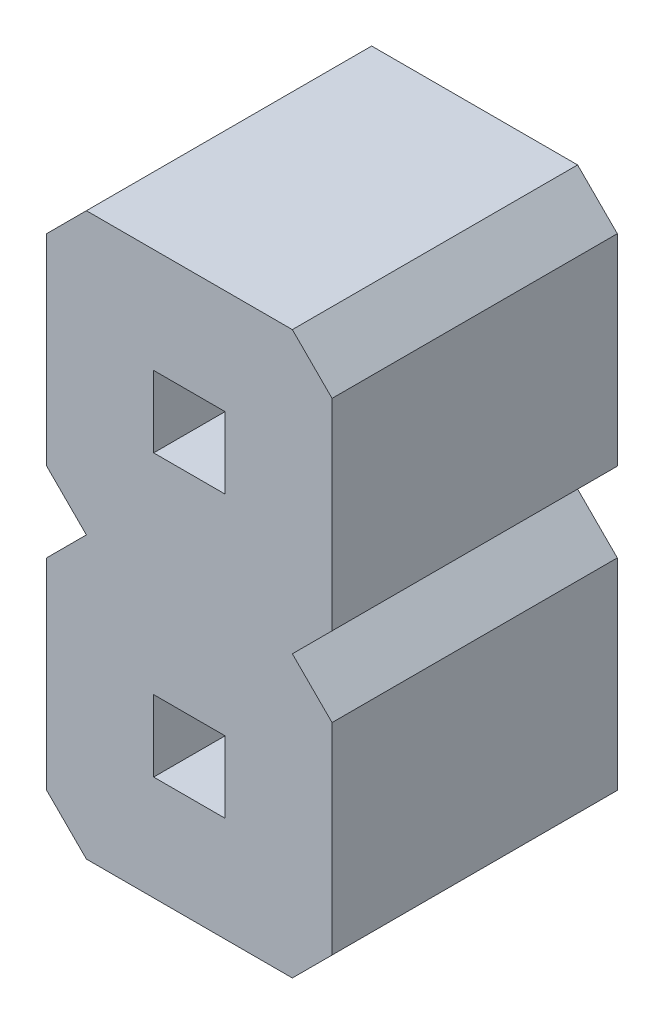
SolidWorks part; units mm, degrees
ref_plane "Alzado" through (0, 0, 0) normal (0, 0, 1) x (1, 0, 0)
ref_plane "Planta" through (0, 0, 0) normal (0, 1, 0) x (1, 0, 0)
ref_plane "Vista lateral" through (0, 0, 0) normal (1, 0, 0) x (0, 0, -1)
sketch "pin_body" plane through (0, 0, 0) normal (0, 0, 1) x (1, 0, 0)
  line L0 (0.9525, -0.932) -> (0, -0.932) construction
  line L1 (0, 2.1464) -> (0, 0.3536)
  line L2 (0, -0.3536) -> (0, -2.1464)
  line L3 (0, -0.3536) -> (0.3536, 0)
  line L4 (1.5885, -1.568) -> (2.541, -1.568) construction
  line L5 (0, 2.1464) -> (0.3536, 2.5)
  line L6 (2.541, -0.3536) -> (2.541, -2.1464)
  line L7 (0.9525, -1.25) -> (0.9525, -0.932) construction
  line L8 (2.541, -2.1464) -> (2.1874, -2.5)
  line L9 (2.1874, 0) -> (2.541, -0.3536)
  line L10 (1.5885, -1.25) -> (1.5885, -1.568) construction
  line L11 (0.3536, -2.5) -> (0, -2.1464)
  line L12 (0.9525, -0.932) -> (1.5885, -0.932)
  line L13 (0.9525, -0.932) -> (0.9525, -1.568)
  line L14 (0.9525, -1.568) -> (1.5885, -1.568)
  line L15 (1.5885, -0.932) -> (1.5885, -1.568)
  line L16 (2.541, 2.1464) -> (2.541, 0.3536)
  line L17 (2.541, 0.3536) -> (2.1874, 0)
  line L18 (2.1874, 2.5) -> (2.541, 2.1464)
  line L19 (0.3536, 0) -> (0, 0.3536)
  line L20 (0.9525, 1.568) -> (1.5885, 1.568)
  line L21 (0.9525, 1.568) -> (0.9525, 0.932)
  line L22 (0.9525, 0.932) -> (1.5885, 0.932)
  line L23 (1.5885, 1.568) -> (1.5885, 0.932)
  line L24 (0.9525, 1.568) -> (0, 1.568) construction
  line L25 (1.5885, 0.932) -> (2.541, 0.932) construction
  line L26 (0.9525, 1.25) -> (0.9525, 1.568) construction
  line L27 (1.5885, 1.25) -> (1.5885, 0.932) construction
  line L28 (0.3536, 2.5) -> (2.1874, 2.5)
  line L168 (2.1874, -2.5) -> (0.3536, -2.5)
  line L170 (0, 17.1464) -> (0, 15.3536) [skipped]
  line L171 (0, 17.1464) -> (0.3536, 17.5) [skipped]
  line L172 (2.541, 17.1464) -> (2.541, 15.3536) [skipped]
  line L173 (2.541, 15.3536) -> (2.1874, 15) [skipped]
  line L174 (2.1874, 17.5) -> (2.541, 17.1464) [skipped]
  line L175 (0.9525, 16.568) -> (1.5885, 16.568) [skipped]
  line L176 (0.9525, 16.568) -> (0.9525, 15.932) [skipped]
  line L177 (0.9525, 15.932) -> (1.5885, 15.932) [skipped]
  line L178 (1.5885, 16.568) -> (1.5885, 15.932) [skipped]
  line L179 (0, 19.6464) -> (0, 17.8536) [skipped]
  line L180 (0, 19.6464) -> (0.3536, 20) [skipped]
  line L181 (2.541, 19.6464) -> (2.541, 17.8536) [skipped]
  line L182 (2.541, 17.8536) -> (2.1874, 17.5) [skipped]
  line L183 (2.1874, 20) -> (2.541, 19.6464) [skipped]
  line L184 (0.3536, 17.5) -> (0, 17.8536) [skipped]
  line L185 (0.9525, 19.068) -> (1.5885, 19.068) [skipped]
  line L186 (0.9525, 19.068) -> (0.9525, 18.432) [skipped]
  line L187 (0.9525, 18.432) -> (1.5885, 18.432) [skipped]
  line L188 (1.5885, 19.068) -> (1.5885, 18.432) [skipped]
  line L189 (0, 22.1464) -> (0, 20.3536) [skipped]
  line L190 (0, 22.1464) -> (0.3536, 22.5) [skipped]
  line L191 (2.541, 22.1464) -> (2.541, 20.3536) [skipped]
  line L192 (2.541, 20.3536) -> (2.1874, 20) [skipped]
  line L193 (2.1874, 22.5) -> (2.541, 22.1464) [skipped]
  line L194 (0.3536, 20) -> (0, 20.3536) [skipped]
  line L195 (0.9525, 21.568) -> (1.5885, 21.568) [skipped]
  line L196 (0.9525, 21.568) -> (0.9525, 20.932) [skipped]
  line L197 (0.9525, 20.932) -> (1.5885, 20.932) [skipped]
  line L198 (1.5885, 21.568) -> (1.5885, 20.932) [skipped]
  line L199 (0, 24.6464) -> (0, 22.8536) [skipped]
  line L200 (0, 24.6464) -> (0.3536, 25) [skipped]
  line L201 (2.541, 24.6464) -> (2.541, 22.8536) [skipped]
  line L202 (2.541, 22.8536) -> (2.1874, 22.5) [skipped]
  line L203 (2.1874, 25) -> (2.541, 24.6464) [skipped]
  line L204 (0.3536, 22.5) -> (0, 22.8536) [skipped]
  line L205 (0.9525, 24.068) -> (1.5885, 24.068) [skipped]
  line L206 (0.9525, 24.068) -> (0.9525, 23.432) [skipped]
  line L207 (0.9525, 23.432) -> (1.5885, 23.432) [skipped]
  line L208 (1.5885, 24.068) -> (1.5885, 23.432) [skipped]
  line L209 (0, 27.1464) -> (0, 25.3536) [skipped]
  line L210 (0, 27.1464) -> (0.3536, 27.5) [skipped]
  line L211 (2.541, 27.1464) -> (2.541, 25.3536) [skipped]
  line L212 (2.541, 25.3536) -> (2.1874, 25) [skipped]
  line L213 (2.1874, 27.5) -> (2.541, 27.1464) [skipped]
  line L214 (0.3536, 25) -> (0, 25.3536) [skipped]
  line L215 (0.9525, 26.568) -> (1.5885, 26.568) [skipped]
  line L216 (0.9525, 26.568) -> (0.9525, 25.932) [skipped]
  line L217 (0.9525, 25.932) -> (1.5885, 25.932) [skipped]
  line L218 (1.5885, 26.568) -> (1.5885, 25.932) [skipped]
  line L219 (0.9525, 16.568) -> (0, 16.568) construction
  line L220 (1.5885, 15.932) -> (2.541, 15.932) construction
  line L221 (0.9525, 16.25) -> (0.9525, 16.568) construction
  line L222 (1.5885, 16.25) -> (1.5885, 15.932) construction
  line L223 (0.9525, 19.068) -> (0, 19.068) construction
  line L224 (1.5885, 18.432) -> (2.541, 18.432) construction
  line L225 (0.9525, 18.75) -> (0.9525, 19.068) construction
  line L226 (1.5885, 18.75) -> (1.5885, 18.432) construction
  line L227 (0.9525, 21.568) -> (0, 21.568) construction
  line L228 (1.5885, 20.932) -> (2.541, 20.932) construction
  line L229 (0.9525, 21.25) -> (0.9525, 21.568) construction
  line L230 (1.5885, 21.25) -> (1.5885, 20.932) construction
  line L231 (0.9525, 24.068) -> (0, 24.068) construction
  line L232 (1.5885, 23.432) -> (2.541, 23.432) construction
  line L233 (0.9525, 23.75) -> (0.9525, 24.068) construction
  line L234 (1.5885, 23.75) -> (1.5885, 23.432) construction
  line L235 (0.9525, 26.568) -> (0, 26.568) construction
  line L236 (1.5885, 25.932) -> (2.541, 25.932) construction
  line L237 (0.9525, 26.25) -> (0.9525, 26.568) construction
  line L238 (1.5885, 26.25) -> (1.5885, 25.932) construction
  line L239 (0, 14.6464) -> (0.3536, 15) [skipped]
  line L240 (2.1874, 15) -> (2.541, 14.6464) [skipped]
  line L241 (0.9525, 14.068) -> (1.5885, 14.068) [skipped]
  line L242 (0.9525, 14.068) -> (0.9525, 13.432) [skipped]
  line L243 (0.9525, 13.432) -> (1.5885, 13.432) [skipped]
  line L244 (1.5885, 14.068) -> (1.5885, 13.432) [skipped]
  line L245 (0.3536, 15) -> (0, 15.3536) [skipped]
  line L246 (0.9525, 14.068) -> (0, 14.068) construction
  line L247 (0.9525, 13.75) -> (0.9525, 14.068) construction
  line L248 (1.5885, 13.75) -> (1.5885, 13.432) construction
  line L249 (2.541, 14.6464) -> (2.541, 12.8536) [skipped]
  line L250 (2.541, 12.8536) -> (2.1874, 12.5) [skipped]
  line L251 (1.5885, 13.432) -> (2.541, 13.432) construction
  line L252 (0, 14.6464) -> (0, 12.8536) [skipped]
  line L253 (0.3536, 12.5) -> (0, 12.8536) [skipped]
  line L254 (0, 7.1464) -> (0.3536, 7.5) [skipped]
  line L255 (0, 9.6464) -> (0, 7.8536) [skipped]
  line L256 (0, 9.6464) -> (0.3536, 10) [skipped]
  line L257 (2.1874, 10) -> (2.541, 9.6464) [skipped]
  line L258 (0.3536, 7.5) -> (0, 7.8536) [skipped]
  line L259 (0.9525, 9.068) -> (1.5885, 9.068) [skipped]
  line L260 (0.9525, 9.068) -> (0.9525, 8.432) [skipped]
  line L261 (0.9525, 8.432) -> (1.5885, 8.432) [skipped]
  line L262 (1.5885, 9.068) -> (1.5885, 8.432) [skipped]
  line L263 (0, 12.1464) -> (0, 10.3536) [skipped]
  line L264 (0, 12.1464) -> (0.3536, 12.5) [skipped]
  line L265 (2.541, 12.1464) -> (2.541, 10.3536) [skipped]
  line L266 (2.541, 10.3536) -> (2.1874, 10) [skipped]
  line L267 (2.1874, 12.5) -> (2.541, 12.1464) [skipped]
  line L268 (0.3536, 10) -> (0, 10.3536) [skipped]
  line L269 (0.9525, 11.568) -> (1.5885, 11.568) [skipped]
  line L270 (0.9525, 11.568) -> (0.9525, 10.932) [skipped]
  line L271 (0.9525, 10.932) -> (1.5885, 10.932) [skipped]
  line L272 (1.5885, 11.568) -> (1.5885, 10.932) [skipped]
  line L273 (0.9525, 9.068) -> (0, 9.068) construction
  line L274 (0.9525, 8.75) -> (0.9525, 9.068) construction
  line L275 (1.5885, 8.75) -> (1.5885, 8.432) construction
  line L276 (0.9525, 11.568) -> (0, 11.568) construction
  line L277 (1.5885, 10.932) -> (2.541, 10.932) construction
  line L278 (0.9525, 11.25) -> (0.9525, 11.568) construction
  line L279 (1.5885, 11.25) -> (1.5885, 10.932) construction
  line L280 (0, 7.1464) -> (0, 5.3536) [skipped]
  line L281 (2.541, 7.1464) -> (2.541, 5.3536) [skipped]
  line L282 (2.541, 5.3536) -> (2.1874, 5) [skipped]
  line L283 (2.1874, 7.5) -> (2.541, 7.1464) [skipped]
  line L284 (0.9525, 6.568) -> (1.5885, 6.568) [skipped]
  line L285 (0.9525, 6.568) -> (0.9525, 5.932) [skipped]
  line L286 (0.9525, 5.932) -> (1.5885, 5.932) [skipped]
  line L287 (1.5885, 6.568) -> (1.5885, 5.932) [skipped]
  line L288 (2.541, 9.6464) -> (2.541, 7.8536) [skipped]
  line L289 (2.541, 7.8536) -> (2.1874, 7.5) [skipped]
  line L290 (0.9525, 6.568) -> (0, 6.568) construction
  line L291 (1.5885, 5.932) -> (2.541, 5.932) construction
  line L292 (0.9525, 6.25) -> (0.9525, 6.568) construction
  line L293 (1.5885, 6.25) -> (1.5885, 5.932) construction
  line L294 (1.5885, 8.432) -> (2.541, 8.432) construction
  line L295 (0, 4.6464) -> (0.3536, 5) [skipped]
  line L296 (2.541, 4.6464) -> (2.541, 2.8536) [skipped]
  line L297 (2.1874, 5) -> (2.541, 4.6464) [skipped]
  line L298 (0.9525, 4.068) -> (1.5885, 4.068) [skipped]
  line L299 (1.5885, 4.068) -> (1.5885, 3.432) [skipped]
  line L300 (0.3536, 5) -> (0, 5.3536) [skipped]
  line L301 (1.5885, 3.432) -> (2.541, 3.432) construction
  line L302 (1.5885, 3.75) -> (1.5885, 3.432) construction
  line L303 (0, 4.6464) -> (0, 2.8536) [skipped]
  line L304 (0.3536, 2.5) -> (0, 2.8536) [skipped]
  line L305 (0.9525, 4.068) -> (0.9525, 3.432) [skipped]
  line L306 (0.9525, 3.432) -> (1.5885, 3.432) [skipped]
  line L307 (0.9525, 3.75) -> (0.9525, 4.068) construction
  line L308 (2.541, 2.8536) -> (2.1874, 2.5) [skipped]
  line L309 (0.9525, 4.068) -> (0, 4.068) construction
  dimension "D1" = 0.318
  dimension "D2" = 0.9525
  dimension "D3" = 0.5
  dimension "D4" = 135
  dimension "D5" = 0.5
  dimension "D6" = 135
  dimension "D7" = 12
extrude "Boss-Extrude1" add sketch "pin_body" along normal blind 2.54
